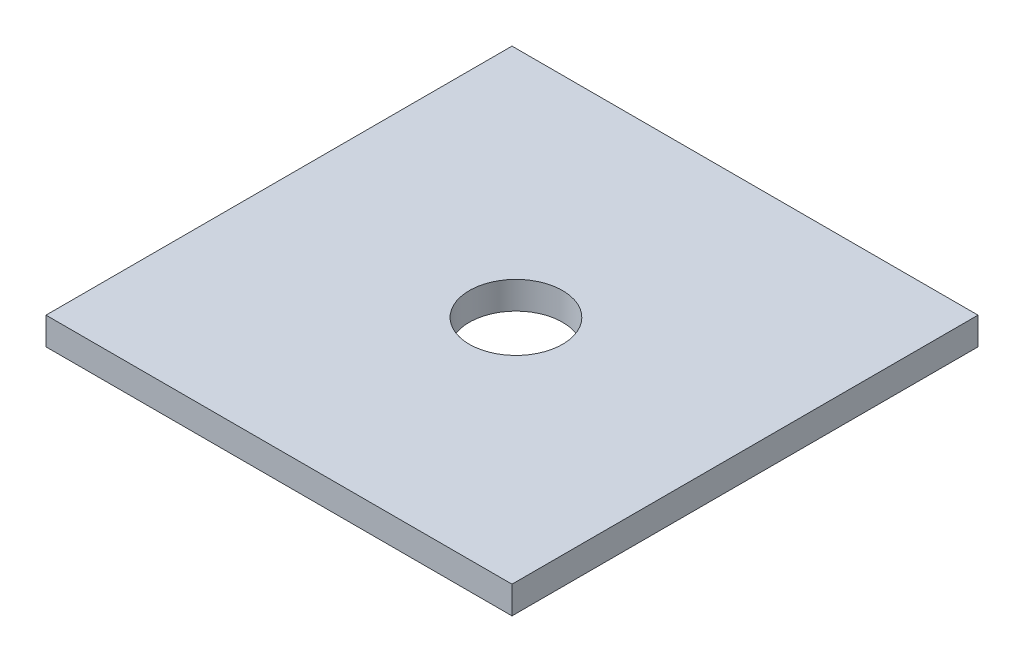
SolidWorks part; units mm, degrees
ref_plane "Front Plane" through (0, 0, 0) normal (0, 0, 1) x (1, 0, 0)
ref_plane "Top Plane" through (0, 0, 0) normal (0, 1, 0) x (1, 0, 0)
ref_plane "Right Plane" through (0, 0, 0) normal (1, 0, 0) x (0, 0, -1)
sketch "Sketch1" plane through (0, 0, 0) normal (0, 1, 0) x (1, 0, 0)
  line L1 (-25.4237, 20.7097) -> (24.5763, 20.7097)
  line L2 (-25.4237, 20.7097) -> (-25.4237, -29.2903)
  line L3 (-25.4237, -29.2903) -> (24.5763, -29.2903)
  line L4 (24.5763, 20.7097) -> (24.5763, -29.2903)
  dimension "D1" = 50
  dimension "D2" = 50
extrude "Boss-Extrude1" add sketch "Sketch1" along normal blind 2.95
sketch "Sketch2" plane through (0, 2.95, 0) normal (0, 1, 0) x (1, 0, 0)
  line L1 (-25.4237, -29.2903) -> (24.5763, -29.2903) construction
  circle A0 centre (0, -4.2903) radius 5
  dimension "D1" = 25
extrude "Cut-Extrude1" cut sketch "Sketch2" against normal blind 6.86
